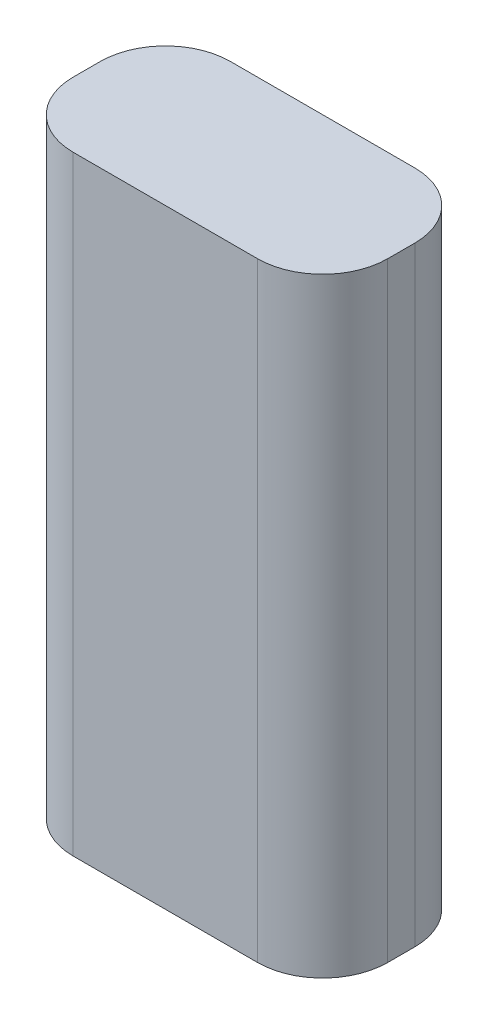
SolidWorks part; units mm, degrees
ref_plane "Front Plane" through (0, 0, 0) normal (0, 0, 1) x (1, 0, 0)
ref_plane "Top Plane" through (0, 0, 0) normal (0, 1, 0) x (1, 0, 0)
ref_plane "Right Plane" through (0, 0, 0) normal (1, 0, 0) x (0, 0, -1)
sketch "Sketch1" plane through (0, 0, 0) normal (0, 0, 1) x (1, 0, 0)
  line L1 (0, 0) -> (36.83, 0)
  line L2 (0, 0) -> (0, -71.374)
  line L3 (0, -71.374) -> (36.83, -71.374)
  line L4 (36.83, 0) -> (36.83, -71.374)
  dimension "D1" = 36.83
  dimension "D2" = 71.374
extrude "Boss-Extrude1" add sketch "Sketch1" along normal blind 18.415
fillet "Fillet1" radius 7.62 4 edges at (0, -35.687, 0) (36.83, -35.687, 0) (0, -35.687, 18.415) (36.83, -35.687, 18.415)
